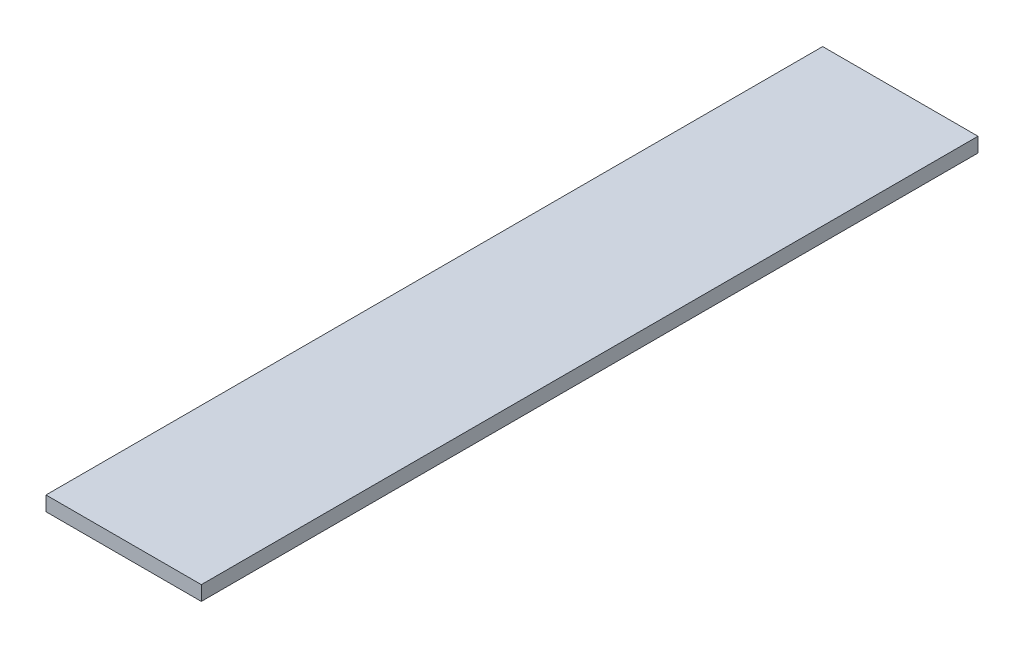
SolidWorks part; units mm, degrees
ref_plane "Front Plane" through (0, 0, 0) normal (0, 0, 1) x (1, 0, 0)
ref_plane "Top Plane" through (0, 0, 0) normal (0, 1, 0) x (1, 0, 0)
ref_plane "Right Plane" through (0, 0, 0) normal (1, 0, 0) x (0, 0, -1)
sketch "Sketch1" plane through (0, 0, 0) normal (0, 1, 0) x (1, 0, 0)
  line L1 (0, 0) -> (50.8, 0)
  line L2 (0, 0) -> (0, -254)
  line L3 (0, -254) -> (50.8, -254)
  line L4 (50.8, 0) -> (50.8, -254)
  dimension "D1" = 254
  dimension "D2" = 50.8
extrude "Boss-Extrude1" add sketch "Sketch1" along normal blind 4.7625 contours L1 L4 L3 L2
